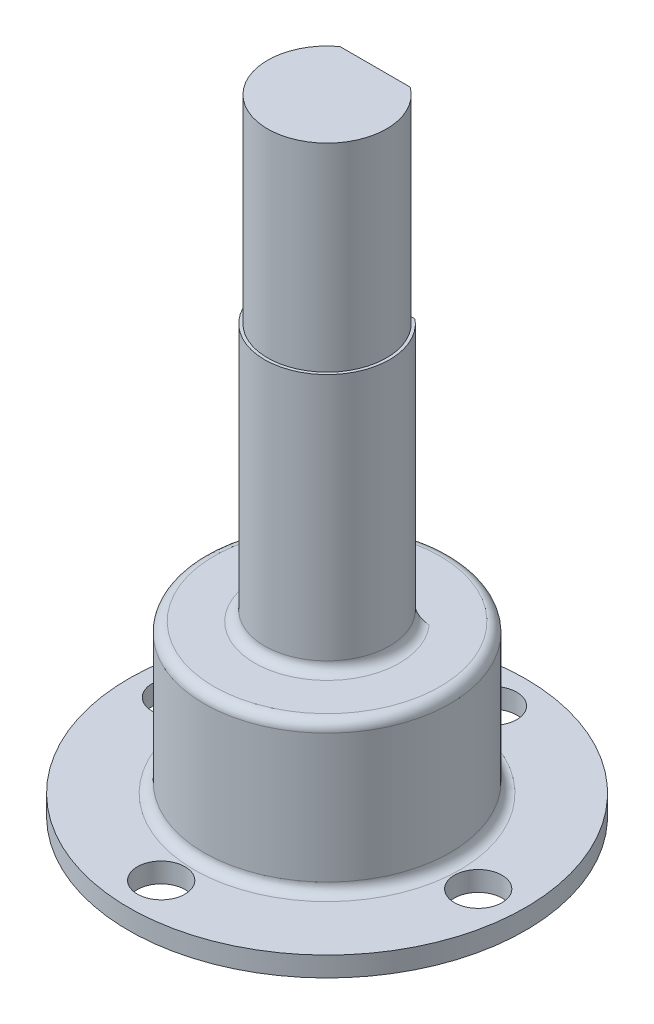
SolidWorks part; units mm, degrees
material "ABS"
ref_plane "Plan de face" through (0, 0, 0) normal (0, 0, 1) x (1, 0, 0)
ref_plane "Plan de dessus" through (0, 0, 0) normal (0, 1, 0) x (1, 0, 0)
ref_plane "Plan de droite" through (0, 0, 0) normal (1, 0, 0) x (0, 0, -1)
sketch "Esquisse2" plane through (0, 0, 0) normal (0, 0, 1) x (1, 0, 0)
  line L0 (0, 31.5) -> (3, 31.5)
  line L3 (6.2, 3) -> (6.2, 1)
  line L4 (6.2, 1) -> (10, 1)
  line L5 (10, 1) -> (10, 0)
  line L6 (10, 0) -> (4.5, 0)
  line L7 (4.5, 0) -> (4.5, 5)
  line L8 (4.5, 5) -> (0, 5)
  line L9 (0, 5) -> (0, 31.5)
  line L11 (3.15, 21.5) -> (3.15, 8.5)
  line L12 (3.15, 8.5) -> (6.2, 8.5)
  line L13 (6.2, 3) -> (6.2, 8.5)
  line L14 (3.15, 21.5) -> (3, 21.5)
  line L15 (3, 21.5) -> (3, 31.5)
  point P2 (1.5, 31.5)
  dimension "D1" = 10
  dimension "D2" = 31.5
  dimension "D3" = 0
  dimension "D4" = 1
  dimension "D5" = 4.5
  dimension "D6" = 2
  dimension "D7" = 8.5
  dimension "D8" = 5
  dimension "D9" = 3.15
  dimension "D10" = 0
  dimension "D11" = 3
  dimension "D12" = 1.7
  dimension "D13" = 10
revolve "Révolution2" add sketch "Esquisse2" angle 360 about L9
sketch "Esquisse3" plane through (0, 31.5, 0) normal (0, 1, 0) x (1, 0, 0)
  line L1 (-3.6413, 2.4219) -> (2.9365, 2.4219)
  line L2 (-3.6413, 2.4219) -> (-3.6413, 3.808)
  line L3 (-3.6413, 3.808) -> (2.9365, 3.808)
  line L4 (2.9365, 2.4219) -> (2.9365, 3.808)
  dimension "D1" = 6.5779
extrude "Enlèv. mat.-Extru.1" cut sketch "Esquisse3" against normal up to surface (23 mm away) contours L4 L3 L2 L1 up to face at (0, 8.5, -3.15)
hole_wizard "M2 Clearance Hole1" positions "Esquisse4" profile "Esquisse5" hole size "M2" standard "ANSI Metric" end condition up to next
sketch "Esquisse4" plane through (0, 1, 0) normal (0, 1, 0) x (1, 0, 0)
  circle A0 centre (0, 0) radius 8 construction
  point P0 (0.3713, 7.9914)
  dimension "D1" = 16
sketch "Esquisse5" plane through (0.3713, 1, -7.9914) normal (1, 0, 0) x (0, 0, 1)
  line L0 (0, 0) -> (0, 1.001)
  line L1 (0, 1.001) -> (1.2, 1.001)
  line L2 (1.2, 1.001) -> (1.2, 0)
  line L5 (1.2, 0) -> (0, 0)
  line L11 (0, -6.35) -> (0, 107.95) construction
  dimension "Diamètre du perçage jusqu'au prochain" = 2.4
  dimension "Profondeur du perçage jusqu'au prochain" = 1.001
pattern_circular "Répétition circulaire1" count 4 over 360 about axis through (0, 0, 0) along (0, 1, 0) of "M2 Clearance Hole1"
fillet "Fillet1" radius 0.5 3 edges at (0, 8.5, -6.2) (0, 1, -6.2) (0, 8.5, 3.15)
